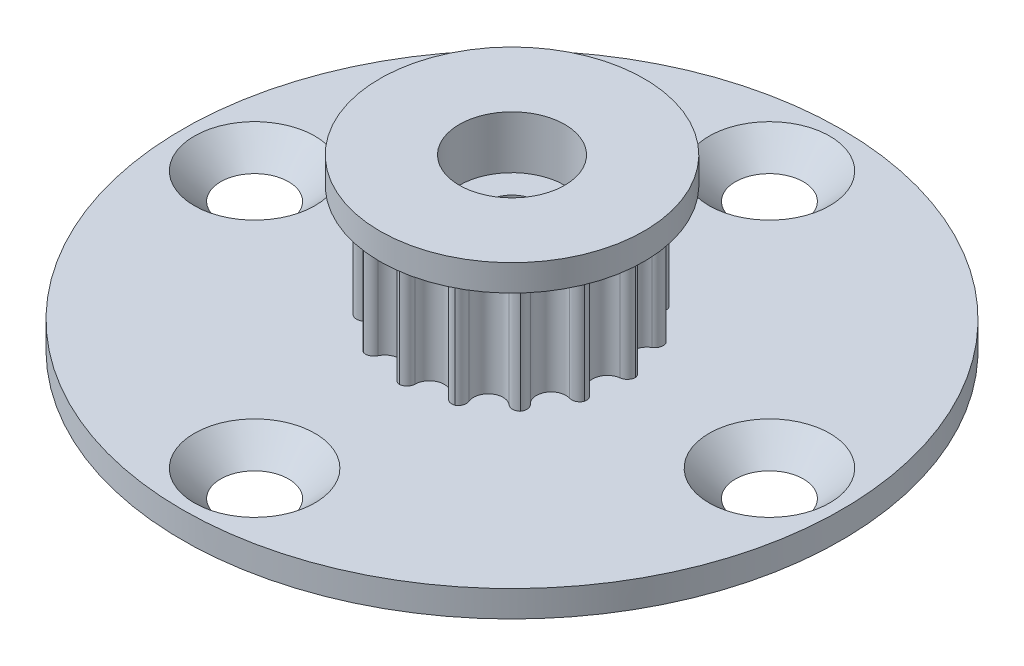
SolidWorks part; units mm, degrees
ref_plane "Front Plane" through (0, 0, 0) normal (0, 0, 1) x (1, 0, 0)
ref_plane "Top Plane" through (0, 0, 0) normal (0, 1, 0) x (1, 0, 0)
ref_plane "Right Plane" through (0, 0, 0) normal (1, 0, 0) x (0, 0, -1)
sketch "Sketch1" plane through (0, 0, 0) normal (0, 1, 0) x (1, 0, 0)
  line L0 (0, 0) -> (0, 6.7802) construction
  line L1 (0, 0) -> (2.6235, 5.8925) construction
  circle A0 centre (0, 0) radius 6.7802 construction
  circle A1 centre (0, 0) radius 5.5602 construction
  circle A2 centre (0, 6.4502) radius 0.89 construction
  circle A5 centre (2.6235, 5.8925) radius 0.89 construction
  arc A6 (0, 5.5602) -> (0.8665, 6.2469) centre (0, 6.4502) ccw
  arc A7 (0.8665, 6.2469) -> (1.461, 6.6209) centre (1.3532, 6.1327) cw
  arc A8 (1.3583, 6.6427) -> (1.7493, 6.0592) centre (1.2581, 6.1529) cw
  arc A9 (2.2615, 5.0795) -> (1.7493, 6.0592) centre (2.6235, 5.8925) cw
  arc A10 (1.461, 6.6209) -> (1.3583, 6.6427) centre (0, 0) cw
  arc A11 (0, 5.5602) -> (2.2615, 5.0795) centre (0, 0) ccw
  dimension "D1" = 13.5604
  dimension "D3" = 1.78
  dimension "D4" = 0.5
  dimension "D2" = 1.22
  dimension "D5" = 24
extrude "Boss-Extrude1" add sketch "Sketch1" along normal mid plane 7.112 contours A6 A11 A9 A8 A7
ref_axis "Axis1" through (0, 3.3, 0) along (0, -1, 0)
pattern_circular "CirPattern1" count 15 over 360 about axis through (0, 0, 0) along (0, 1, 0) of "Boss-Extrude1"
sketch "Sketch2" plane through (0, 0, 0) normal (1, 0, 0) x (0, 0, -1)
  line L10 (0, 3.5) -> (7.9549, 3.5) construction
  line L11 (0, 3.5) -> (0, 5.0875) construction
  line L12 (0, 5.0875) -> (7.9549, 5.0875) construction
  line L15 (7.9549, 3.5) -> (7.9549, 5.0875) construction
  line L20 (0, 3.3) -> (0, -3.3) construction
  line L22 (7.9549, 5.0875) -> (0, 5.0875)
  line L23 (7.9549, 5.0875) -> (7.9549, 3.5)
  line L24 (7.9549, 3.5) -> (0, 3.5)
  line L25 (0, 5.0875) -> (0, 3.5)
  dimension "D1" = 1.5875
  dimension "D2" = 7.9549
  dimension "D3" = 3.5
revolve "Revolve3" add sketch "Sketch2" angle 360 about axis through (0, 3.3, 0) along (0, -1, 0)
mirror "Mirror1" about plane through (0, 0, 0) normal (0, 1, 0) of "Revolve3"
sketch "Sketch9" plane through (0, -5.0875, 0) normal (0, -1, 0) x (1, 0, 0)
  circle A0 centre (0, 0) radius 19.8438
  circle A1 centre (0, 0) radius 1.5
  dimension "D1" = 3
  dimension "D2" = 39.6875
extrude "Boss-Extrude2" add sketch "Sketch9" against normal up to surface (1.5875 mm away) up to face at (0, -3.5, 0)
sketch "Sketch3" plane through (0, 0, 0) normal (0, 1, 0) x (1, 0, 0)
  circle A0 centre (-15.5, 0) radius 1.7462
  circle A3 centre (0, 15.5) radius 1.7462
  circle A4 centre (15.5, 0) radius 1.7463
  circle A5 centre (0, -15.5) radius 1.7462
  dimension "D3" = 3.4925
  dimension "D1" = 15.5
  dimension "D4" = 4
extrude "Cut-Extrude1" cut sketch "Sketch3" against normal through all both and the other way through all
ref_axis "Axis2" through (-15.5, -5.0875, 0) along (0, 1, 0)
sketch "Sketch6" plane through (0, 0, 0) normal (0, 0, 1) x (1, 0, 0)
  line L0 (-19.1322, -3.5) -> (-11.8678, -3.5) construction
  line L1 (-13.7538, -3.5) -> (-17.2462, -3.5) construction
  line L2 (-11.8678, -3.5) -> (-15.5, -7.1322)
  line L3 (-15.5, -7.1322) -> (-19.1322, -3.5) construction
  line L4 (-18.548, -4.0842) -> (-12.452, -4.0842) construction
  line L5 (-17.2462, -3.998) -> (-13.7538, -3.998) construction
  line L8 (-15.5, -7.1322) -> (-15.5, -3.5)
  line L9 (-15.5, -3.5) -> (-11.8678, -3.5)
  line L10 (-15.5, -5.0875) -> (-15.5, -3.5) construction
  line L12 (-17.2462, -3.5) -> (-17.2462, -5.0875) construction
  line L13 (-13.7538, -5.0875) -> (-13.7538, -3.5) construction
  point P2 (-15.5, -3.998)
  dimension "D1" = 6.096
  dimension "D2" = 0.5842
revolve "Cut-Revolve2" cut sketch "Sketch6" angle 360 about axis through (-15.5, -5.0875, 0) along (0, 1, 0)
pattern_circular "CirPattern2" count 4 over 360 about axis through (0, 0, 0) along (0, 1, 0) of "Cut-Revolve2"
sketch "Sketch12" plane through (0, 5.0875, 0) normal (0, 1, 0) x (1, 0, 0)
  circle A0 centre (0, 0) radius 3.175
  dimension "D1" = 6.35
extrude "Cut-Extrude2" cut sketch "Sketch12" against normal blind 3.175 from surface at 0 starting at face at (0, 5.0875, 7.9549)
sketch "Sketch13" plane through (0, 1.9125, 0) normal (0, 1, 0) x (1, 0, 0)
  circle A0 centre (0, 0) radius 1.525
  dimension "D1" = 3.05
extrude "Cut-Extrude4" cut sketch "Sketch13" against normal through all contours A0
equation "\"TEETH_NUM\" = 15"
equation "\"TOOTH_PITCH\"= 3mm"
equation "\"PITCH_LINE_OFFSET\"= .015in"
equation "\"DIAMETER_PER_GROOVE\"= \"OUTSIDE_DIAMETER\" / \"TEETH_NUM\" * 1in"
equation "\"PITCH_DIAMETER\"= ( ( \"TEETH_NUM\" * 3 - 1.31 ) / 3.1415 + .415 ) * 1mm"
equation "\"OUTSIDE_DIAMETER\"= \"PITCH_DIAMETER\" - \"PITCH_LINE_OFFSET\" * 2"
equation "\"D1@Sketch1\"=\"OUTSIDE_DIAMETER\""
equation "\"TOOTH_HEIGHT\"= 1.22mm"
equation "\"D2@Sketch1\"=\"TOOTH_HEIGHT\""
equation "\"TOOTH_DIAMETER\"= 1.78mm"
equation "\"INTERNAL_RADIUS\"= .5mm"
equation "\"D3@Sketch1\"=\"TOOTH_DIAMETER\""
equation "\"D5@Sketch1\"=360 / \"TEETH_NUM\""
equation "\"D4@Sketch1\"=\"INTERNAL_RADIUS\""
equation "\"D1@CirPattern1\"=\"TEETH_NUM\""
equation "\"BELT_GAP\"= 7mm"
equation "\"D2@Sketch2\"=\"PITCH_DIAMETER\"/2+1/32"
equation "\"D3@Sketch2\"=\"BELT_GAP\"/2"
